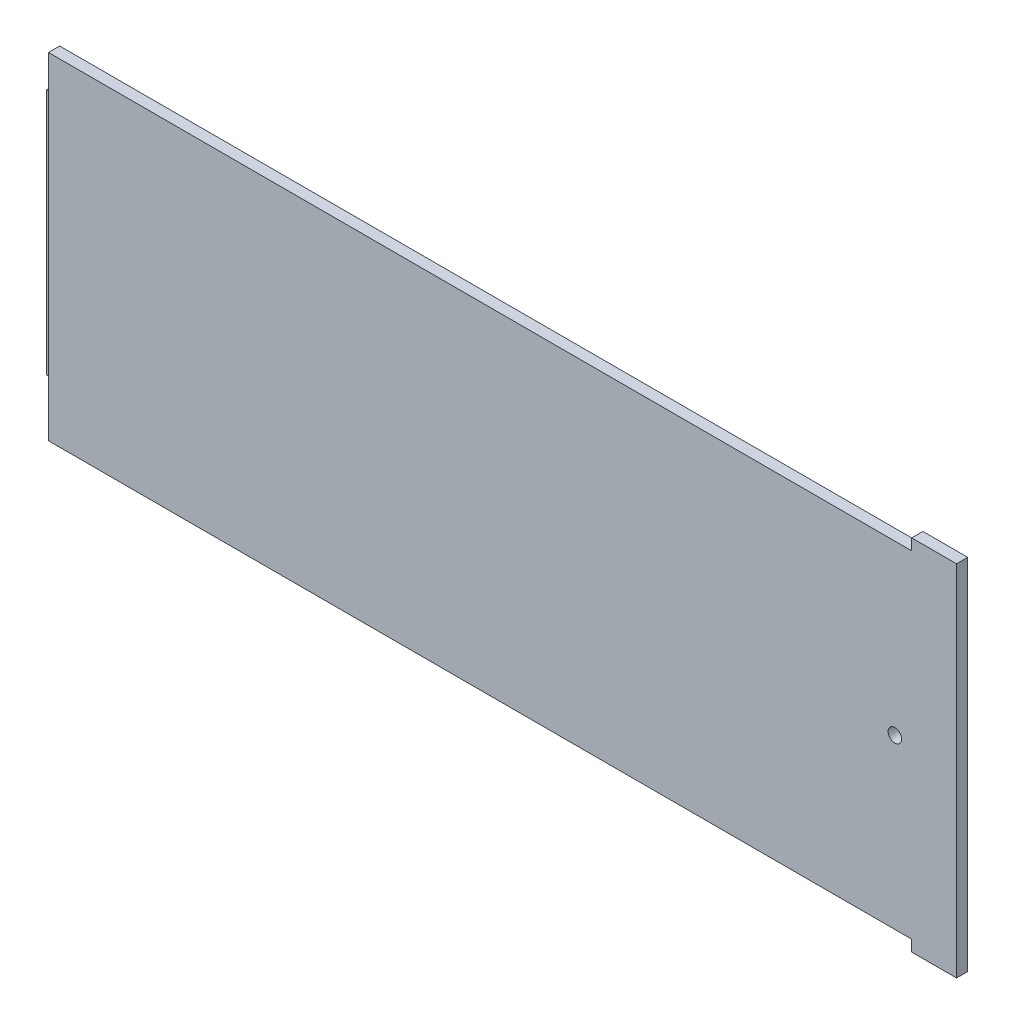
SolidWorks part; units mm, degrees
ref_plane "Front Plane" through (0, 0, 0) normal (0, 0, 1) x (1, 0, 0)
ref_plane "Top Plane" through (0, 0, 0) normal (0, 1, 0) x (1, 0, 0)
ref_plane "Right Plane" through (0, 0, 0) normal (1, 0, 0) x (0, 0, -1)
sketch "Sketch1" plane through (0, 0, 0) normal (0, 0, 1) x (1, 0, 0)
  line L1 (0, 0) -> (202.5, 0)
  line L2 (0, 0) -> (0, 75)
  line L3 (0, 75) -> (202.5, 75)
  line L4 (202.5, 0) -> (202.5, 75)
  dimension "D1" = 202.5
  dimension "D2" = 75
extrude "Boss-Extrude7" add sketch "Sketch1" along normal blind 2.5
sketch "Sketch9" plane through (0, 75, 0) normal (0, 1, 0) x (1, 0, 0)
  line L0 (202.5, -2.5) -> (0, -2.5) construction
  line L1 (192.5, -2.5) -> (202.5, -2.5)
  line L2 (192.5, -2.5) -> (192.5, 0)
  line L3 (192.5, 0) -> (202.5, 0)
  line L4 (202.5, -2.5) -> (202.5, 0)
  dimension "D1" = 10
extrude "Boss-Extrude8" add sketch "Sketch9" along normal blind 2.5
sketch "Sketch10" plane through (0, 0, 0) normal (0, -1, 0) x (1, 0, 0)
  line L0 (0, 0) -> (202.5, 0) construction
  line L1 (192.5, 0) -> (202.5, 0)
  line L2 (192.5, 0) -> (192.5, 2.5)
  line L3 (192.5, 2.5) -> (202.5, 2.5)
  line L4 (202.5, 0) -> (202.5, 2.5)
  dimension "D1" = 10
extrude "Boss-Extrude9" add sketch "Sketch10" along normal blind 2.5
sketch "Sketch11" plane through (0, 0, 2.5) normal (0, 0, 1) x (1, 0, 0)
  line L6 (192.5, 75) -> (192.5, 0) construction
  line L7 (205, 37.5) -> (187.5, 37.5) construction
  line L8 (202.5, -2.5) -> (202.5, 77.5) construction
  circle A0 centre (188.75, 37.5) radius 1.5
  dimension "D2" = 3
  dimension "D1" = 13.75
extrude "Cut-Extrude3" cut sketch "Sketch11" against normal up to surface (2.5 mm away) up to face at (146.875, 37.5, 0)
sketch "Sketch12" plane through (0, 0, 0) normal (0, 0, -1) x (-1, 0, 0)
  line L0 (0, 75) -> (0, 0) construction
  line L1 (0, 65) -> (-2.5, 65)
  line L2 (0, 65) -> (0, 10)
  line L3 (0, 10) -> (-2.5, 10)
  line L4 (-2.5, 65) -> (-2.5, 10)
  line L5 (-192.5, 75) -> (0, 75) construction
  line L6 (0, 0) -> (-192.5, 0) construction
  dimension "D1" = 10
  dimension "D2" = 10
  dimension "D3" = 55
  dimension "D4" = 2.5
extrude "Boss-Extrude10" add sketch "Sketch12" along normal blind 2.5
sketch "Sketch13" plane through (0, 0, 0) normal (-1, 0, 0) x (0, 0, 1)
  line L1 (0, 65) -> (-2.5, 65)
  line L2 (0, 65) -> (0, 10)
  line L3 (0, 10) -> (-2.5, 10)
  line L4 (-2.5, 65) -> (-2.5, 10)
  dimension "D1" = 55
  dimension "D2" = 2.5
extrude "Boss-Extrude11" add sketch "Sketch13" along normal blind 3
